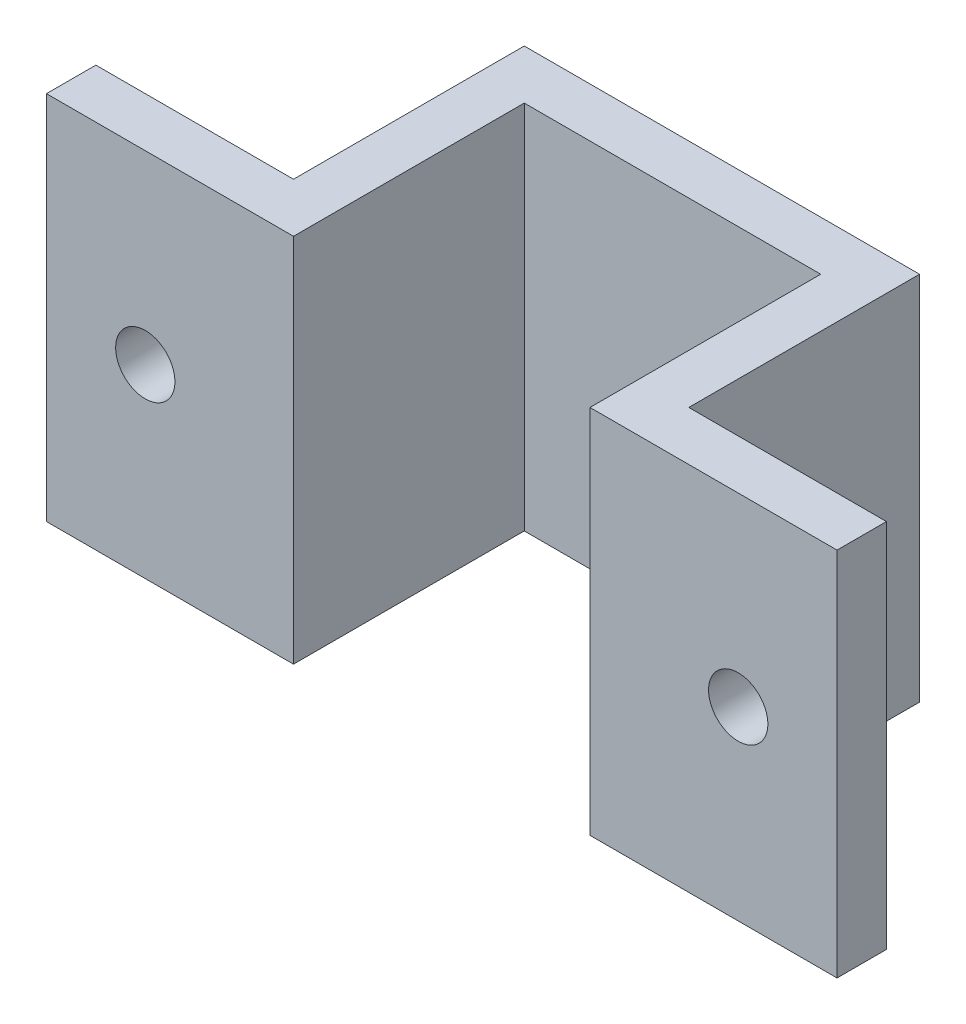
SolidWorks part; units mm, degrees
ref_plane "Front" through (0, 0, 0) normal (0, 0, 1) x (1, 0, 0)
ref_plane "Top" through (0, 0, 0) normal (0, 1, 0) x (1, 0, 0)
ref_plane "Right" through (0, 0, 0) normal (1, 0, 0) x (0, 0, -1)
sketch "Sketch1" plane through (0, 0, 0) normal (0, 1, 0) x (1, 0, 0)
  line L0 (0, 0) -> (0, 13.2307) construction
  line L1 (7.62, 0) -> (20.32, 0)
  line L2 (20.32, 0) -> (20.32, 2.54)
  line L3 (20.32, 2.54) -> (10.16, 2.54)
  line L4 (10.16, 2.54) -> (10.16, 14.4018)
  line L5 (10.16, 14.4018) -> (-10.16, 14.4018)
  line L6 (-10.16, 14.4018) -> (-10.16, 2.54)
  line L7 (-10.16, 2.54) -> (-20.32, 2.54)
  line L8 (-20.32, 2.54) -> (-20.32, 0)
  line L9 (-20.32, 0) -> (-7.62, 0)
  line L10 (-7.62, 0) -> (-7.62, 11.8618)
  line L11 (-7.62, 11.8618) -> (7.62, 11.8618)
  line L12 (7.62, 11.8618) -> (7.62, 0)
  dimension "D1" = 2.54
  dimension "D2" = 15.24
  dimension "D3" = 11.8618
  dimension "D4" = 2.54
  dimension "D5" = 2.54
  dimension "D6" = 12.7
extrude "Boss-Extrude1" add sketch "Sketch1" along normal blind 19.05
sketch "Sketch2" plane through (0, 0, -2.54) normal (0, 0, -1) x (-1, 0, 0)
  line L0 (20.32, 9.525) -> (-20.32, 9.525) construction
  line L1 (20.32, 19.05) -> (20.32, 0) construction
  line L2 (-20.32, 19.05) -> (-20.32, 0) construction
  line L3 (-15.24, 19.05) -> (-15.24, 0) construction
  line L4 (-20.32, 19.05) -> (-10.16, 19.05) construction
  line L5 (-20.32, 0) -> (-10.16, 0) construction
  line L6 (15.24, 19.05) -> (15.24, 0) construction
  line L7 (10.16, 19.05) -> (20.32, 19.05) construction
  line L8 (10.16, 0) -> (20.32, 0) construction
  circle A0 centre (15.24, 9.525) radius 1.524
  circle A1 centre (-15.24, 9.525) radius 1.524
  dimension "D1" = 3.048
extrude "Cut-Extrude1" cut sketch "Sketch2" against normal through all
